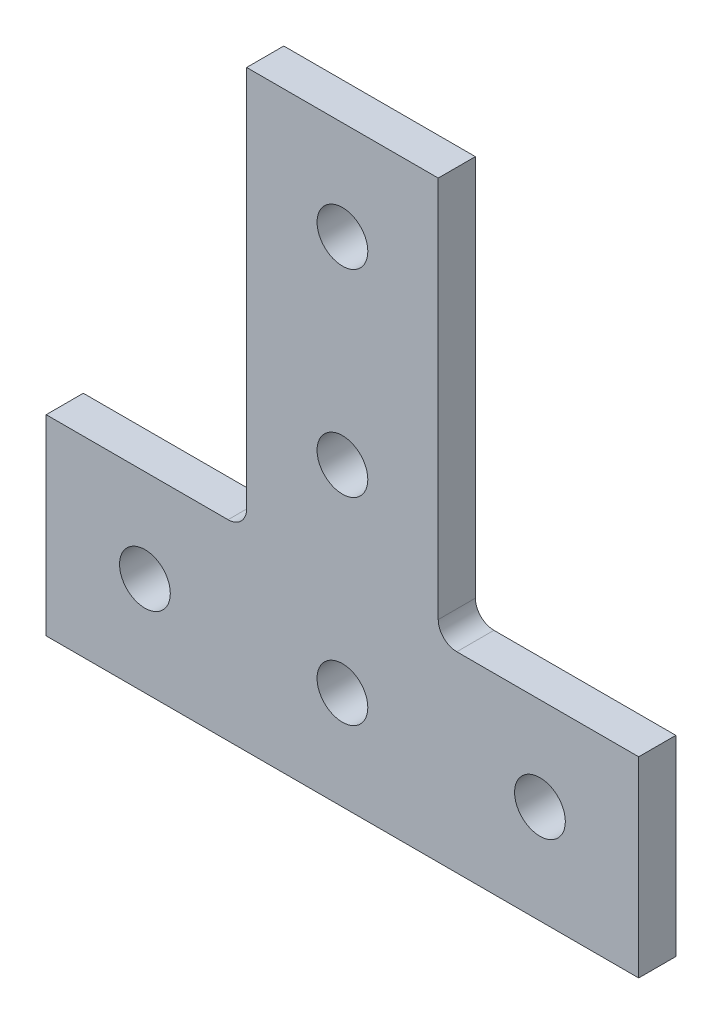
SolidWorks part; units mm, degrees
ref_plane "Front Plane" through (0, 0, 0) normal (0, 0, 1) x (1, 0, 0)
ref_plane "Top Plane" through (0, 0, 0) normal (0, 1, 0) x (1, 0, 0)
ref_plane "Right Plane" through (0, 0, 0) normal (1, 0, 0) x (0, 0, -1)
ref_plane "Plane1" through (0, 0, 0) normal (0, 0, 1) x (1, 0, 0)
sketch "Sketch1" plane through (0, 0, 0) normal (0, 0, 1) x (1, 0, 0)
  line L0 (-38.1, 0) -> (38.1, 0)
  line L1 (38.1, 0) -> (38.1, 24.638)
  line L2 (38.1, 24.638) -> (14.7066, 24.638)
  line L3 (12.319, 27.0256) -> (12.319, 76.2)
  line L4 (12.319, 76.2) -> (-12.319, 76.2)
  line L5 (-12.319, 76.2) -> (-12.319, 27.0256)
  line L6 (-14.7066, 24.638) -> (-38.1, 24.638)
  line L7 (-38.1, 24.638) -> (-38.1, 0)
  arc A0 (14.7066, 24.638) -> (12.319, 27.0256) centre (14.7066, 27.0256) cw
  arc A1 (-12.319, 27.0256) -> (-14.7066, 24.638) centre (-14.7066, 27.0256) cw
  circle A2 centre (25.4, 12.7) radius 3.2639
  circle A3 centre (0, 38.1) radius 3.2639
  circle A4 centre (0, 63.5) radius 3.2639
  circle A5 centre (0, 12.7) radius 3.2639
  circle A6 centre (-25.4, 12.7) radius 3.2639
extrude "Boss-Extrude1" add sketch "Sketch1" along normal blind 4.7752
